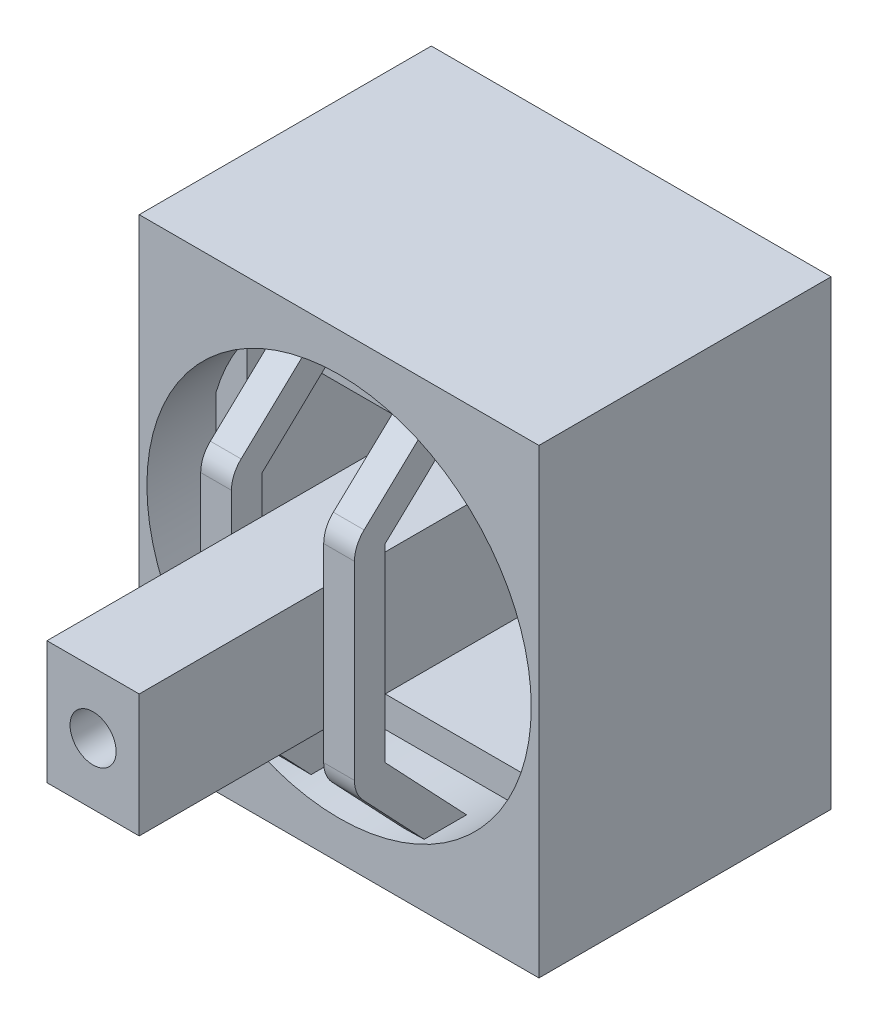
SolidWorks part; units mm, degrees
ref_plane "Plano frontal" through (0, 0, 0) normal (0, 0, 1) x (1, 0, 0)
ref_plane "Plano superior" through (0, 0, 0) normal (0, 1, 0) x (1, 0, 0)
ref_plane "Plano direito" through (0, 0, 0) normal (1, 0, 0) x (0, 0, -1)
sketch "Esboço1" plane through (0, 0, 0) normal (0, 0, 1) x (1, 0, 0)
  line L1 (-6.5, -7.5) -> (6.5, -7.5)
  line L2 (-6.5, -7.5) -> (-6.5, 7.5)
  line L3 (-6.5, 7.5) -> (6.5, 7.5)
  line L4 (6.5, -7.5) -> (6.5, 7.5)
  line L5 (-6.5, -7.5) -> (6.5, 7.5) construction
  line L6 (-6.5, 7.5) -> (6.5, -7.5) construction
  point P0 (0, 0)
  dimension "D1" = 13
  dimension "D2" = 15
extrude "Ressalto-extrusão1" add sketch "Esboço1" against normal blind 9.5
sketch "Esboço3" plane through (0, 0, 0) normal (0, 0, 1) x (1, 0, 0)
  circle A0 centre (0, 0) radius 6.25
  dimension "D1" = 12.5
extrude "Corte-extrusão1" cut sketch "Esboço3" against normal through all
sketch "Esboço2" plane through (0, 0, 0) normal (0, 0, 1) x (1, 0, 0)
  line L1 (-1.5, -2) -> (1.5, -2)
  line L2 (-1.5, -2) -> (-1.5, 2)
  line L3 (-1.5, 2) -> (1.5, 2)
  line L4 (1.5, -2) -> (1.5, 2)
  line L5 (-1.5, -2) -> (1.5, 2) construction
  line L6 (-1.5, 2) -> (1.5, -2) construction
  circle A0 centre (0, 0) radius 0.75
  dimension "D1" = 1.5
  dimension "D2" = 4
  dimension "D3" = 3
extrude "Ressalto-extrusão2" add sketch "Esboço2" along normal blind 8 and the other way up to surface (9.5 mm away) other way up to face at (6.25, 0, -9.5)
sketch "Esboço4" plane through (-6.5, 0, 0) normal (-1, 0, 0) x (0, 0, 1)
  line L0 (-6.5, 0.25) -> (-9.5, 0.25) construction
  line L2 (-6.5, 2.25) -> (-6.5, -1.75)
  line L3 (-6.5, -1.75) -> (-4.8493, -0.75)
  line L4 (-4.8493, -0.75) -> (-4.8493, 1.25)
  line L5 (-4.8493, 1.25) -> (-6.5, 2.25)
  line L8 (-9.5, 7.5) -> (-9.5, -7.5) construction
  line L9 (-9.5, 7.5) -> (0, 7.5) construction
  point P8 (-6.5, 0.25)
  dimension "D1" = 7.25
  dimension "D2" = 1.93
  dimension "D3" = 1.93
  dimension "D4" = 4
  dimension "D5" = 2
extrude "Ressalto-extrusão3" add sketch "Esboço4" along normal blind 1.5
sketch "Esboço5" plane through (0, 0, -9.5) normal (0, 0, -1) x (-1, 0, 0)
  line L0 (-5, 4) -> (5, 4)
  line L1 (-6, -5) -> (6, -5)
  line L2 (-6, -5) -> (-6, 5)
  line L3 (-6, 5) -> (6, 5)
  line L4 (6, -5) -> (6, 5)
  line L5 (-6, -5) -> (6, 5) construction
  line L6 (-6, 5) -> (6, -5) construction
  line L7 (5, -4) -> (5, 4)
  line L8 (-5, -4) -> (5, -4)
  line L9 (-5, -4) -> (-5, 4)
  point P0 (0, 0)
  dimension "D1" = 10
  dimension "D2" = 12
  dimension "D3" = 1
extrude "Ressalto-extrusão4" add sketch "Esboço5" against normal blind 7.5
sketch "Esboço6" plane through (-1.5, 0, 0) normal (-1, 0, 0) x (0, 0, 1)
  line L0 (-1, 7.5) -> (-1, 6.5)
  line L1 (-9.5, 7.5) -> (0, 7.5) construction
  line L2 (-1, 6.5) -> (2, 3.6672)
  line L3 (2, 3.6672) -> (2, -3.3328)
  line L4 (2, -3.3328) -> (-1, -6.5)
  line L5 (-1, -6.5) -> (-1, -7.5)
  line L6 (-9.5, -7.5) -> (0, -7.5) construction
  line L7 (0, 7.5) -> (0, -7.5) construction
  line L8 (-2, 7.5) -> (-2, 6.0689)
  line L9 (-2, 6.0689) -> (1, 3.2361)
  line L10 (1, 3.2361) -> (1, -2.9344)
  line L11 (1, -2.9344) -> (-2, -6.1016)
  line L12 (-2, -6.1016) -> (-2, -7.5)
  line L13 (-2, 7.5) -> (-1, 7.5)
  line L14 (-2, -7.5) -> (-1, -7.5)
  dimension "D1" = 1
  dimension "D2" = 1
  dimension "D3" = 1
  dimension "D4" = 1
  dimension "D5" = 3
  dimension "D6" = 7
  dimension "D7" = 1
extrude "Ressalto-extrusão5" add sketch "Esboço6" along normal blind 1
mirror "Espelhar1" about plane through (0, 0, 0) normal (1, 0, 0) of "Ressalto-extrusão5"
fillet "Filete1" radius 1 4 edges at (2, 3.6672, 2) (2, -3.3328, 2) (-2, -3.3328, 2) (-2, 3.6672, 2)
